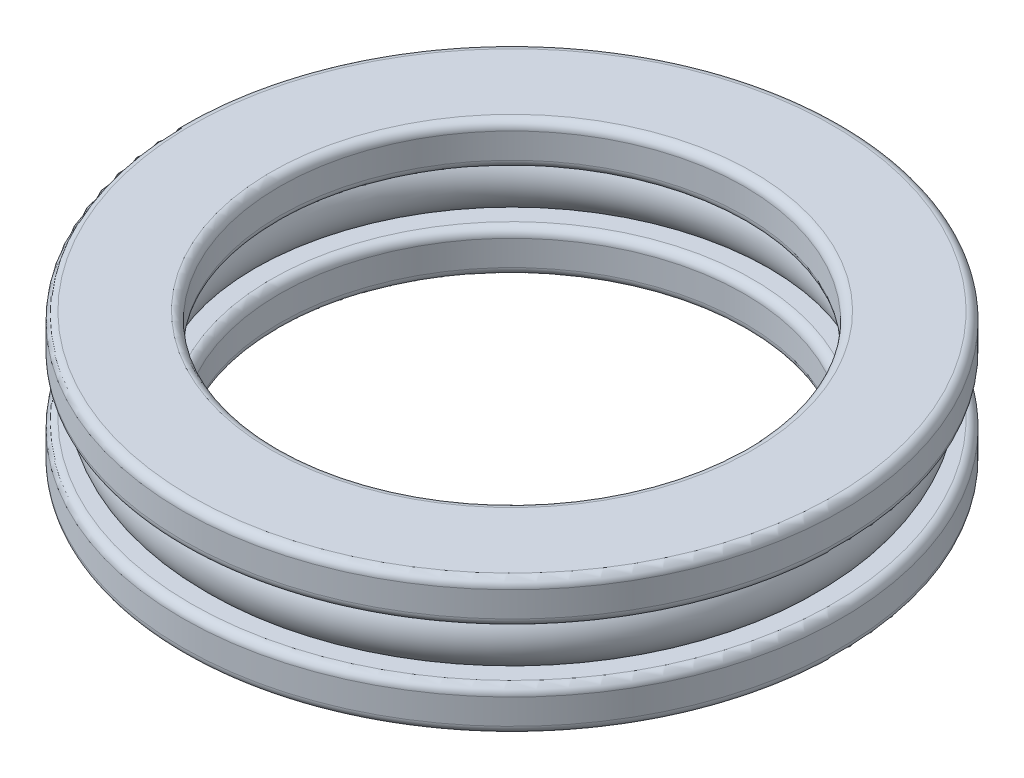
SolidWorks part; units mm, degrees
ref_plane "Front Plane" through (0, 0, 0) normal (0, 0, 1) x (1, 0, 0)
ref_plane "Top Plane" through (0, 0, 0) normal (0, 1, 0) x (1, 0, 0)
ref_plane "Right Plane" through (0, 0, 0) normal (1, 0, 0) x (0, 0, -1)
sketch "Sketch1" plane through (0, 0, 0) normal (0, 0, 1) x (1, 0, 0)
  line L0 (33.25, 0) -> (0, 0) construction
  line L1 (0, 0) -> (0, 43.8759) construction
  line L2 (27.5, -3) -> (30.6042, -3)
  line L15 (27.5, 8) -> (39, 8)
  line L16 (27.5, 8) -> (27.5, 3)
  line L21 (27.5, -8) -> (39, -8)
  line L22 (39, 8) -> (39, 3)
  line L23 (27.5, 8) -> (39, -8) construction
  line L24 (27.5, -8) -> (39, 8) construction
  line L25 (27.5, 3) -> (30.6042, 3)
  line L26 (39, -3) -> (39, -8)
  line L27 (27.5, -3) -> (27.5, -8)
  line L28 (35.8958, -3) -> (39, -3)
  line L29 (35.8958, 3) -> (39, 3)
  arc A0 (35.8958, -3) -> (35.8958, 3) centre (33.25, 0) ccw
  arc A1 (30.6042, 3) -> (30.6042, -3) centre (33.25, 0) ccw
  dimension "D3" = 8
  dimension "D1" = 16
  dimension "D2" = 11.5
  dimension "D4" = 5
  dimension "D5" = 5
  dimension "D6" = 27.5
revolve "Revolve1" add sketch "Sketch1" angle 360 about L1
fillet "Fillet1" radius 1 8 edges at (0, -3, -27.5) (0, 3, -27.5) (0, 3, -39) (0, -3, -39) (0, -8, -39) (0, -8, -27.5) (0, 8, -27.5) (0, 8, -39)
